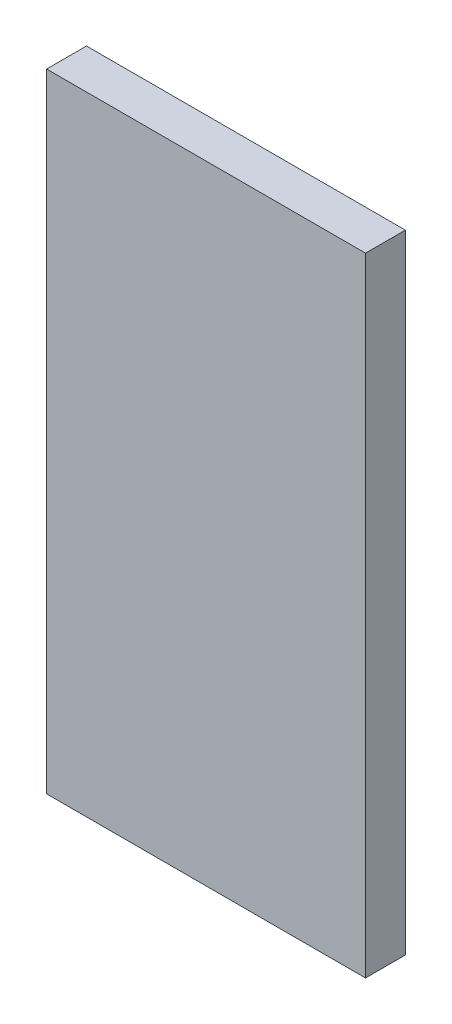
SolidWorks part; units mm, degrees
ref_plane "Front Plane" through (0, 0, 0) normal (0, 0, 1) x (1, 0, 0)
ref_plane "Top Plane" through (0, 0, 0) normal (0, 1, 0) x (1, 0, 0)
ref_plane "Right Plane" through (0, 0, 0) normal (1, 0, 0) x (0, 0, -1)
sketch "Sketch1" plane through (0, 0, 0) normal (0, 0, 1) x (1, 0, 0)
  line L1 (0, 0) -> (50.8, 0)
  line L2 (0, 0) -> (0, -100)
  line L3 (0, -100) -> (50.8, -100)
  line L4 (50.8, 0) -> (50.8, -100)
  dimension "D1" = 100
  dimension "D2" = 50.8
extrude "Boss-Extrude1" add sketch "Sketch1" along normal blind 6.35
